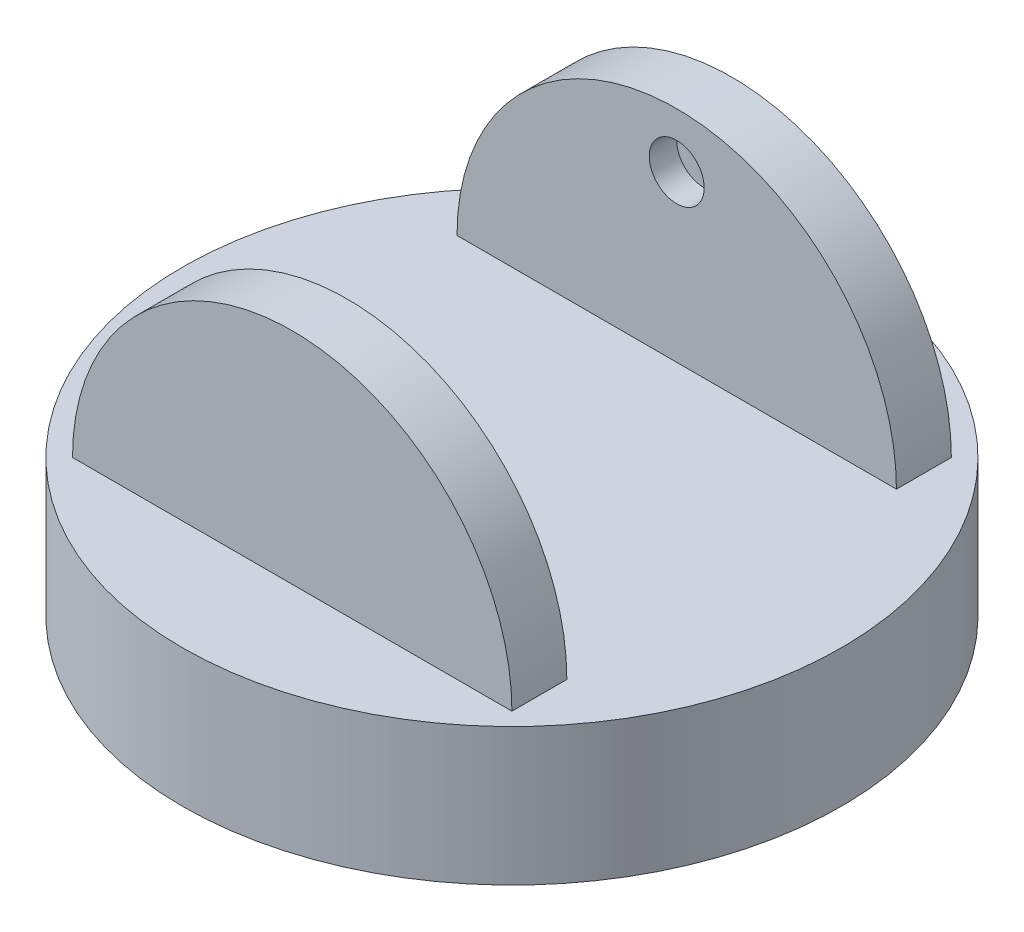
SolidWorks part; units mm, degrees
ref_plane "Front Plane" through (0, 0, 0) normal (0, 0, 1) x (1, 0, 0)
ref_plane "Top Plane" through (0, 0, 0) normal (0, 1, 0) x (1, 0, 0)
ref_plane "Right Plane" through (0, 0, 0) normal (1, 0, 0) x (0, 0, -1)
sketch "Sketch1" plane through (0, 0, 0) normal (0, 1, 0) x (1, 0, 0)
  circle A0 centre (0, 0) radius 60
  dimension "D1" = 120
extrude "Boss-Extrude1" add sketch "Sketch1" along normal blind 25
sketch "Sketch2" plane through (0, 0, 0) normal (0, 0, 1) x (1, 0, 0)
  line L0 (60, 25) -> (-60, 25) construction
  line L1 (-40, 25) -> (0, 25)
  line L2 (0, 25) -> (40, 25)
  arc A0 (-40, 25) -> (40, 25) centre (0, 25) cw
  dimension "D2" = 40
  dimension "D1" = 0
extrude "Boss-Extrude2" add sketch "Sketch2" along normal blind 40
ref_plane "Plane1" through (0, 0, 0) normal (0, 0, -1) x (-1, 0, 0)
mirror "Mirror1" about plane through (0, 0, 0) normal (0, 0, -1) of "Boss-Extrude2"
sketch "Sketch3" plane through (0, 25, 0) normal (0, 1, 0) x (1, 0, 0)
  line L1 (-40, 30) -> (40, 30)
  line L2 (-40, 30) -> (-40, -30)
  line L3 (-40, -30) -> (40, -30)
  line L4 (40, 30) -> (40, -30)
  line L5 (-40, 30) -> (40, -30) construction
  line L6 (-40, -30) -> (40, 30) construction
  point P0 (0, 0)
  dimension "D1" = 60
  dimension "D2" = 80
extrude "Cut-Extrude1" cut sketch "Sketch3" along normal blind 60
sketch "Sketch4" plane through (0, 0, -30) normal (0, 0, 1) x (1, 0, 0)
  circle A0 centre (0, 55) radius 5
  dimension "D2" = 10
  dimension "D1" = 55
extrude "Cut-Extrude2" cut sketch "Sketch4" against normal blind 5
mirror "Mirror2" about plane through (0, 0, 0) normal (0, 0, -1) of "Cut-Extrude2"
